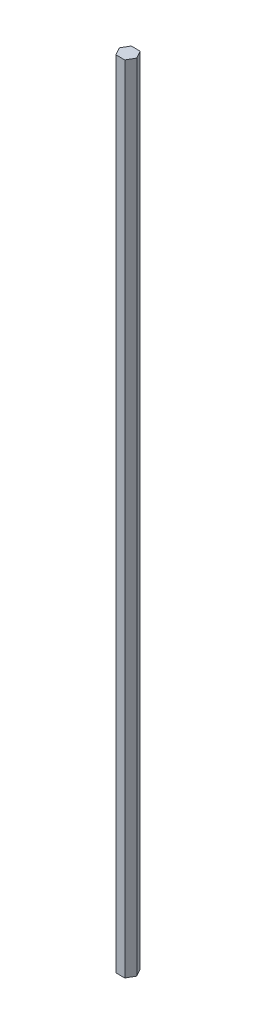
SolidWorks part; units mm, degrees
ref_plane "Front Plane" through (0, 0, 0) normal (0, 0, 1) x (1, 0, 0)
ref_plane "Top Plane" through (0, 0, 0) normal (0, 1, 0) x (1, 0, 0)
ref_plane "Right Plane" through (0, 0, 0) normal (1, 0, 0) x (0, 0, -1)
sketch "Sketch1" plane through (0, 0, 0) normal (0, 1, 0) x (1, 0, 0)
  line L1 (3.6662, -6.35) -> (7.3323, 0)
  line L2 (7.3323, 0) -> (3.6662, 6.35)
  line L3 (3.6662, 6.35) -> (-3.6662, 6.35)
  line L4 (-3.6662, 6.35) -> (-7.3323, 0)
  line L5 (-7.3323, 0) -> (-3.6662, -6.35)
  line L6 (-3.6662, -6.35) -> (3.6662, -6.35)
  circle A0 centre (0, 0) radius 6.35 construction
  point P1 (3.488, 6.4496)
  dimension "D1" = 12.7
extrude "Boss-Extrude1" add sketch "Sketch1" along normal blind 660.4
